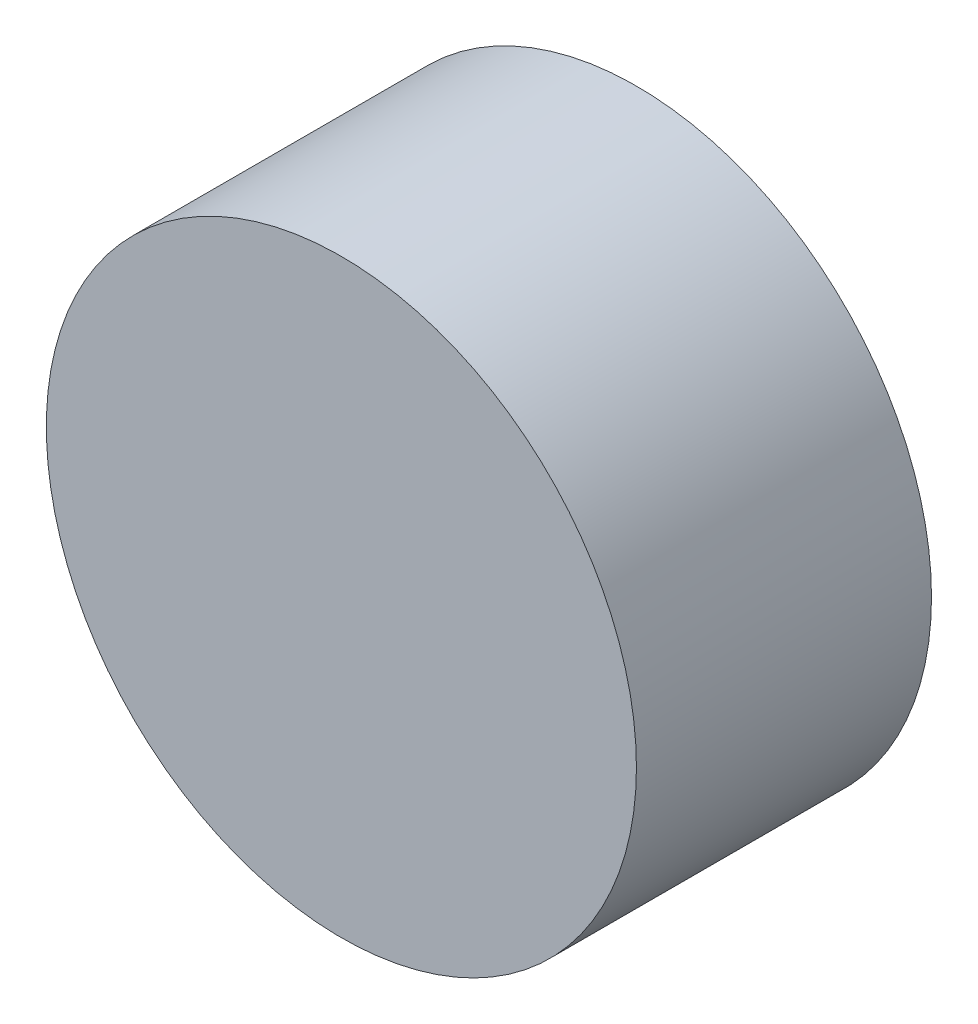
SolidWorks part; units mm, degrees
ref_plane "Ebene vorne" through (0, 0, 0) normal (0, 0, 1) x (1, 0, 0)
ref_plane "Ebene oben" through (0, 0, 0) normal (0, 1, 0) x (1, 0, 0)
ref_plane "Ebene rechts" through (0, 0, 0) normal (1, 0, 0) x (0, 0, -1)
sketch "Skizze1" plane through (0, 0, 0) normal (0, 0, 1) x (1, 0, 0)
  circle A0 centre (0, 0) radius 50
  dimension "D1" = 100
extrude "Aufsatz-Linear austragen1" add sketch "Skizze1" along normal blind 50
sketch "Skizze4" plane through (0, 0, 50) normal (0, 0, 1) x (1, 0, 0)
  line L0 (0, 0) -> (0, 64.896) construction
  line L1 (-1.776, 41.1043) -> (1.776, 41.1043)
  line L2 (1.776, 41.1043) -> (2.6566, 45.8376)
  line L3 (2.6566, 45.8376) -> (5.1884, 50.6808)
  line L4 (5.1884, 50.6808) -> (-5.1884, 50.6808)
  line L5 (-2.6566, 45.8376) -> (-5.1884, 50.6808)
  line L6 (-1.776, 41.1043) -> (-2.6566, 45.8376)
  circle A0 centre (0, 0) radius 50
  point P9 (0, 50.6808)
  point P11 (0, 41.1043)
sketch "Skizze7" plane through (0, 0, 50) normal (0, 0, 1) x (1, 0, 0)
  circle A0 centre (0, 0) radius 50
curve "Spirale/Helix1" pitch 500 height 50 turns 0.1
